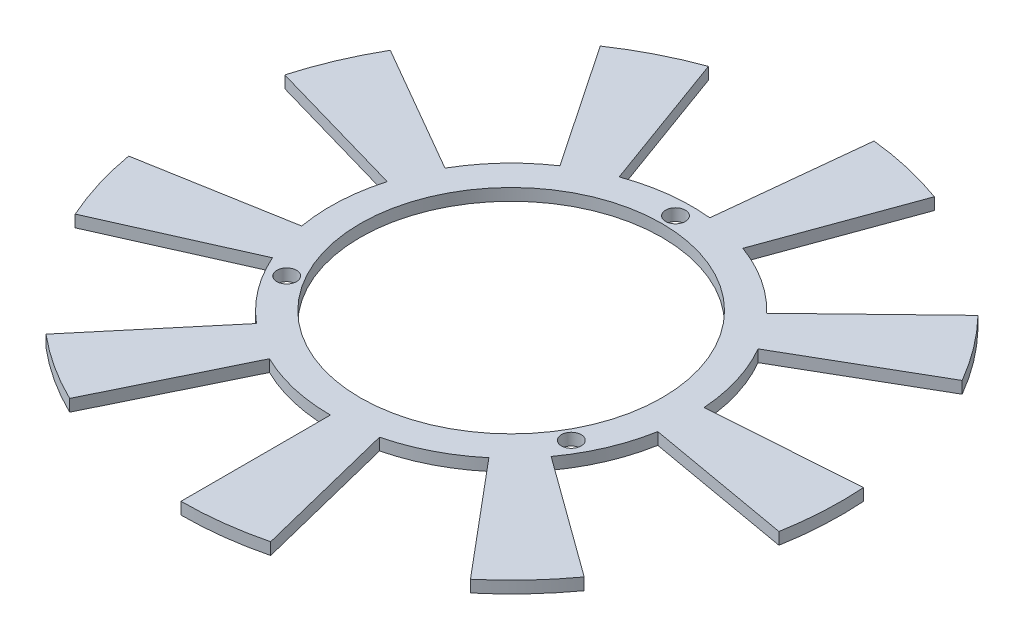
SolidWorks part; units mm, degrees
material "AISI 1010 Steel, hot rolled bar"
ref_plane "Front Plane" through (0, 0, 0) normal (0, 0, 1) x (1, 0, 0)
ref_plane "Top Plane" through (0, 0, 0) normal (0, 1, 0) x (1, 0, 0)
ref_plane "Right Plane" through (0, 0, 0) normal (1, 0, 0) x (0, 0, -1)
sketch "Sketch1" plane through (0, 0, 0) normal (0, 1, 0) x (1, 0, 0)
  circle A0 centre (0, 0) radius 25.25
  dimension "D1" = 50.5
extrude "Extrude-Thin1" add sketch "Sketch1" against normal blind 2 thin
sketch "Sketch2" plane through (0, 0, 0) normal (0, 1, 0) x (1, 0, 0)
  line L0 (0, -30.25) -> (0, 30.25) construction
  line L1 (0, 0) -> (23.8157, -13.75) construction
  line L2 (0, 0) -> (-23.8157, -13.75) construction
  circle A0 centre (0, 27.5) radius 1.65
  circle A1 centre (0, 0) radius 30.25 construction
  circle A4 centre (0, 0) radius 27.5 construction
  circle A7 centre (23.8157, -13.75) radius 1.65
  circle A8 centre (-23.8157, -13.75) radius 1.65
  dimension "D1" = 55
  dimension "D2" = 3.3
  dimension "D3" = 120
  dimension "D4" = 120
extrude "Cut-Extrude3" cut sketch "Sketch2" against normal blind 10
sketch "Sketch5" plane through (0, -2, 0) normal (0, -1, 0) x (1, 0, 0)
  line L0 (0, 0) -> (0, 35.9971) construction
  line L1 (0, 0) -> (8.2512, 33.0937) construction
  line L2 (0, 55.25) -> (0, 30.25)
  line L3 (7.3181, 29.3514) -> (13.3662, 53.6088)
  line L4 (35.514, 42.324) -> (19.4443, 23.1728)
  line L5 (24.4728, 17.7805) -> (44.6982, 32.4751)
  line L6 (54.4106, 9.5941) -> (29.7904, 5.2529)
  line L7 (30.1763, -2.1101) -> (55.1154, -3.854)
  line L8 (47.8479, -27.625) -> (26.1973, -15.125)
  line L9 (21.76, -21.0134) -> (39.7435, -38.3799)
  line L10 (18.8966, -51.918) -> (10.3461, -28.4257)
  line L11 (3.162, -30.0843) -> (5.7752, -54.9473)
  line L12 (-18.8966, -51.918) -> (-10.3461, -28.4257)
  line L13 (-16.9156, -25.0784) -> (-30.8954, -45.8043)
  line L14 (-47.8479, -27.625) -> (-26.1973, -15.125)
  line L15 (-29.0782, -8.338) -> (-53.1097, -15.229)
  line L16 (-54.4106, 9.5941) -> (-29.7904, 5.2529)
  line L17 (-27.6348, 12.3038) -> (-50.4734, 22.4722)
  line L52 (-35.514, 42.324) -> (-19.4443, 23.1728)
  line L53 (-13.2607, 27.1885) -> (-24.22, 49.6584)
  circle A0 centre (0, 0) radius 30.25 construction
  arc A1 (7.3181, 29.3514) -> (0, 30.25) centre (0, 0) ccw
  arc A2 (13.3662, 53.6088) -> (0, 55.25) centre (0, 0) ccw
  arc A3 (44.6982, 32.4751) -> (35.514, 42.324) centre (0, 0) ccw
  arc A4 (24.4728, 17.7805) -> (19.4443, 23.1728) centre (0, 0) ccw
  arc A5 (55.1154, -3.854) -> (54.4106, 9.5941) centre (0, 0) ccw
  arc A6 (30.1763, -2.1101) -> (29.7904, 5.2529) centre (0, 0) ccw
  arc A7 (39.7435, -38.3799) -> (47.8479, -27.625) centre (0, 0) ccw
  arc A8 (21.76, -21.0134) -> (26.1973, -15.125) centre (0, 0) ccw
  arc A9 (5.7752, -54.9473) -> (18.8966, -51.918) centre (0, 0) ccw
  arc A10 (3.162, -30.0843) -> (10.3461, -28.4257) centre (0, 0) ccw
  arc A11 (-30.8954, -45.8043) -> (-18.8966, -51.918) centre (0, 0) ccw
  arc A12 (-16.9156, -25.0784) -> (-10.3461, -28.4257) centre (0, 0) ccw
  arc A13 (-53.1097, -15.229) -> (-47.8479, -27.625) centre (0, 0) ccw
  arc A14 (-29.0782, -8.338) -> (-26.1973, -15.125) centre (0, 0) ccw
  arc A15 (-50.4734, 22.4722) -> (-54.4106, 9.5941) centre (0, 0) ccw
  arc A16 (-27.6348, 12.3038) -> (-29.7904, 5.2529) centre (0, 0) ccw
  arc A51 (-24.22, 49.6584) -> (-35.514, 42.324) centre (0, 0) ccw
  arc A52 (-13.2607, 27.1885) -> (-19.4443, 23.1728) centre (0, 0) ccw
  point P87 (0, 0)
  dimension "D2" = 25
  dimension "D1" = 14
  dimension "D3" = 9
extrude "Boss-Extrude1" add sketch "Sketch5" against normal blind 2
